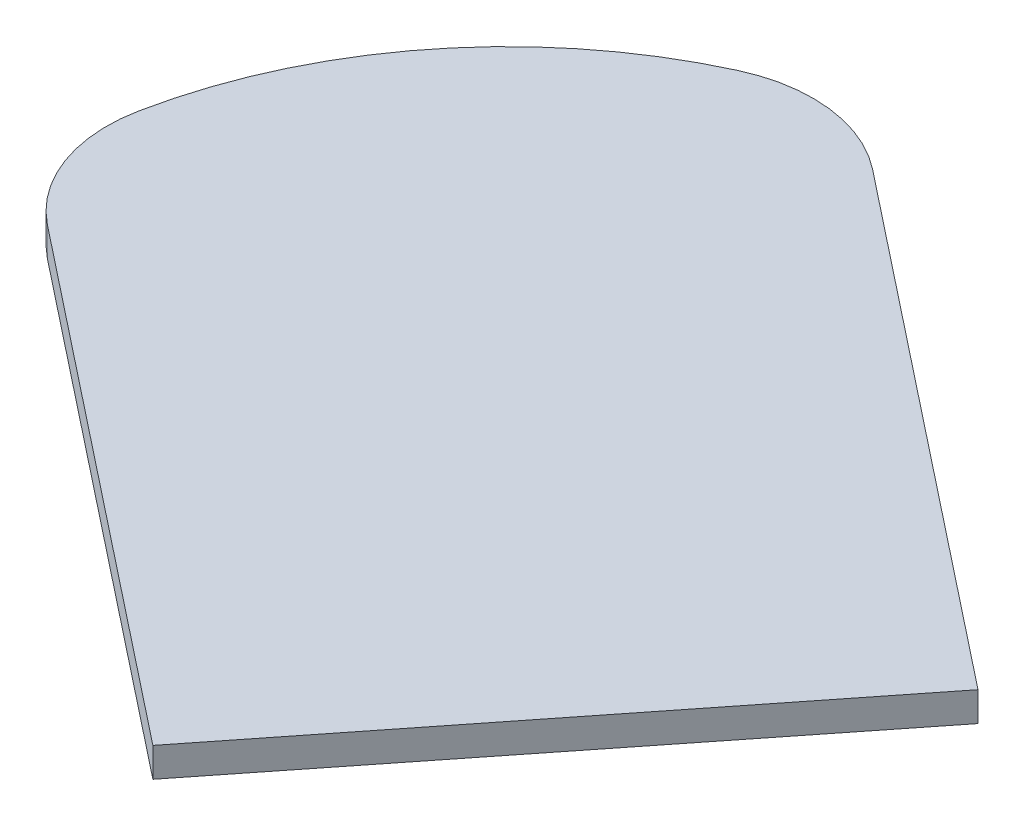
SolidWorks part; units mm, degrees
ref_plane "Płaszczyzna XY" through (0, 0, 0) normal (0, 0, 1) x (1, 0, 0)
ref_plane "Płaszczyzna XZ" through (0, 0, 0) normal (0, 1, 0) x (1, 0, 0)
ref_plane "Płaszczyzna YZ" through (0, 0, 0) normal (1, 0, 0) x (0, 0, -1)
sketch "Sketch1" plane through (0, 0, 0) normal (0, 1, 0) x (1, 0, 0)
  line L0 (-34.272, 2.0226) -> (0.0212, -25.0878)
  line L1 (0.0212, -25.0878) -> (24.8278, 6.291)
  line L2 (24.8278, 6.291) -> (-9.4654, 33.4015)
  arc A0 (-37.8768, 11.8255) -> (-34.272, 2.0226) centre (-28.0704, 9.8674) ccw
  arc A1 (-9.4654, 33.4015) -> (-19.8356, 34.6465) centre (-15.6671, 25.5568) ccw
  arc A2 (-19.8356, 34.6465) -> (-37.8768, 11.8255) centre (-6.4963, 5.5594) ccw
  dimension "D1" = 10
  dimension "D2" = 32
  dimension "D3" = 15.5752
  dimension "D4" = 24.8278
  dimension "D5" = 6.4963
  dimension "D6" = 9.4654
  dimension "D7" = 2.0226
extrude "Boss-Extrude1" add sketch "Sketch1" along normal blind 2
